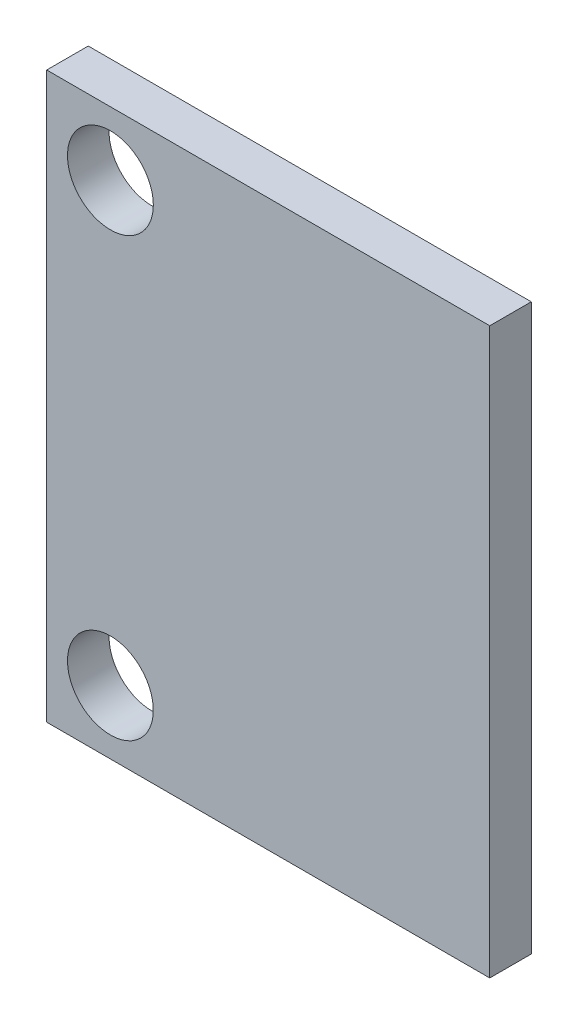
SolidWorks part; units mm, degrees
ref_plane "Front Plane" through (0, 0, 0) normal (0, 0, 1) x (1, 0, 0)
ref_plane "Top Plane" through (0, 0, 0) normal (0, 1, 0) x (1, 0, 0)
ref_plane "Right Plane" through (0, 0, 0) normal (1, 0, 0) x (0, 0, -1)
sketch "Sketch1" plane through (0, 0, 0) normal (0, 0, 1) x (1, 0, 0)
  line L0 (-8, 0) -> (8, 0) construction
  line L1 (8, -10.2) -> (-8, -10.2)
  line L2 (8, -10.2) -> (8, 10.2)
  line L3 (8, 10.2) -> (-8, 10.2)
  line L4 (-8, -10.2) -> (-8, 10.2)
  line L5 (8, -10.2) -> (-8, 10.2) construction
  line L6 (8, 10.2) -> (-8, -10.2) construction
  line L11 (-8, 10.2) -> (-5.7, 10.2) construction
  line L12 (-8, 10.2) -> (-8, 7.9) construction
  line L13 (-8, 7.9) -> (-5.7, 7.9) construction
  line L14 (-5.7, 10.2) -> (-5.7, 7.9) construction
  circle A0 centre (-5.7, 7.9) radius 1.55
  circle A1 centre (-5.7, -7.9) radius 1.55
  point P0 (0, 0)
  dimension "D7" = 3.1
  dimension "D1" = 20.4
  dimension "D2" = 16
  dimension "D5" = 2.3
  dimension "D6" = 2.3
extrude "Boss-Extrude1" add sketch "Sketch1" along normal blind 1.5
